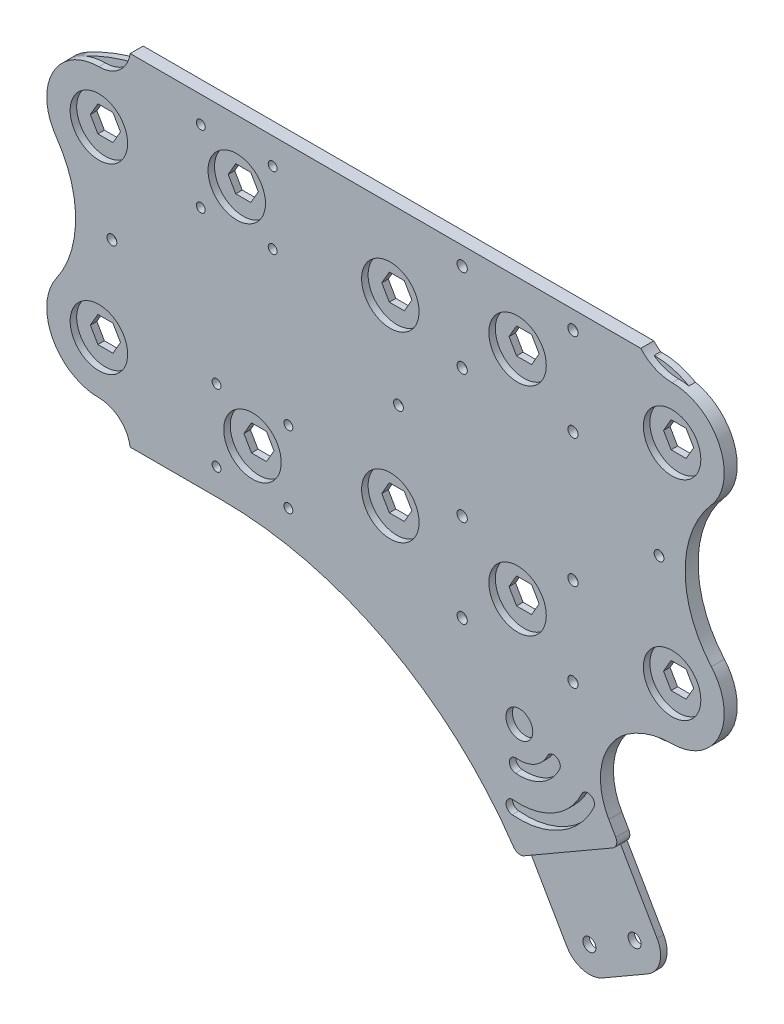
SolidWorks part; units mm, degrees
material "1060 Alloy"
ref_plane "Front Plane" through (0, 0, 0) normal (0, 0, 1) x (1, 0, 0)
ref_plane "Top Plane" through (0, 0, 0) normal (0, 1, 0) x (1, 0, 0)
ref_plane "Right Plane" through (0, 0, 0) normal (1, 0, 0) x (0, 0, -1)
sketch "Sketch1" plane through (0, 0, 0) normal (0, 0, 1) x (1, 0, 0)
  line L9 (183.022, 31.75) -> (225.0336, 31.75)
  line L10 (183.022, 31.75) -> (183.022, 73.7616)
  line L11 (183.022, 73.7616) -> (225.0336, 73.7616)
  line L12 (225.0336, 31.75) -> (225.0336, 73.7616)
  line L13 (183.022, 31.75) -> (225.0336, 73.7616) construction
  line L14 (183.022, 73.7616) -> (225.0336, 31.75) construction
  line L15 (17.8512, 0) -> (50000, 0) construction
  line L16 (46.1727, 31.75) -> (88.1843, 31.75)
  line L17 (46.1727, 31.75) -> (46.1727, 73.7616)
  line L18 (46.1727, 73.7616) -> (88.1843, 73.7616)
  line L19 (88.1843, 31.75) -> (88.1843, 73.7616)
  line L20 (46.1727, 31.75) -> (88.1843, 73.7616) construction
  line L21 (46.1727, 73.7616) -> (88.1843, 31.75) construction
  line L22 (207.694, 59.1058) -> (200.3617, 59.1058)
  line L23 (200.3617, 59.1058) -> (196.6955, 52.7558)
  line L24 (196.6955, 52.7558) -> (200.3617, 46.4058)
  line L25 (200.3617, 46.4058) -> (207.694, 46.4058)
  line L26 (207.694, 46.4058) -> (211.3602, 52.7558)
  line L27 (211.3602, 52.7558) -> (207.694, 59.1058)
  line L28 (74.5108, 52.7558) -> (70.8447, 59.1058)
  line L29 (70.8447, 59.1058) -> (63.5123, 59.1058)
  line L30 (63.5123, 59.1058) -> (59.8461, 52.7558)
  line L31 (59.8461, 52.7558) -> (63.5123, 46.4058)
  line L32 (63.5123, 46.4058) -> (70.8447, 46.4058)
  line L33 (70.8447, 46.4058) -> (74.5108, 52.7558)
  line L34 (3.6662, 50.8) -> (-3.6662, 50.8)
  line L35 (-3.6662, 50.8) -> (-7.3323, 44.45)
  line L36 (-7.3323, 44.45) -> (-3.6662, 38.1)
  line L37 (-3.6662, 38.1) -> (3.6662, 38.1)
  line L38 (3.6662, 38.1) -> (7.3323, 44.45)
  line L39 (7.3323, 44.45) -> (3.6662, 50.8)
  line L40 (282.994, 57.15) -> (275.6617, 57.15)
  line L41 (275.6617, 57.15) -> (271.9955, 50.8)
  line L42 (271.9955, 50.8) -> (275.6617, 44.45)
  line L43 (275.6617, 44.45) -> (282.994, 44.45)
  line L44 (282.994, 44.45) -> (286.6602, 50.8)
  line L45 (286.6602, 50.8) -> (282.994, 57.15)
  line L46 (53.8347, -73.7616) -> (95.8463, -31.75) construction
  line L47 (53.8347, -31.75) -> (95.8463, -73.7616) construction
  line L48 (183.022, -73.7616) -> (225.0336, -31.75) construction
  line L49 (183.022, -31.75) -> (225.0336, -73.7616) construction
  line L50 (286.6602, -50.8) -> (282.994, -57.15)
  line L51 (282.994, -44.45) -> (286.6602, -50.8)
  line L52 (275.6617, -44.45) -> (282.994, -44.45)
  line L53 (271.9955, -50.8) -> (275.6617, -44.45)
  line L54 (275.6617, -57.15) -> (271.9955, -50.8)
  line L55 (282.994, -57.15) -> (275.6617, -57.15)
  line L56 (7.3323, -44.45) -> (3.6662, -50.8)
  line L57 (3.6662, -38.1) -> (7.3323, -44.45)
  line L58 (-3.6662, -38.1) -> (3.6662, -38.1)
  line L59 (-7.3323, -44.45) -> (-3.6662, -38.1)
  line L60 (-3.6662, -50.8) -> (-7.3323, -44.45)
  line L61 (3.6662, -50.8) -> (-3.6662, -50.8)
  line L62 (78.5067, -46.4058) -> (82.1729, -52.7558)
  line L63 (71.1743, -46.4058) -> (78.5067, -46.4058)
  line L64 (67.5082, -52.7558) -> (71.1743, -46.4058)
  line L65 (71.1743, -59.1058) -> (67.5082, -52.7558)
  line L66 (78.5067, -59.1058) -> (71.1743, -59.1058)
  line L67 (82.1729, -52.7558) -> (78.5067, -59.1058)
  line L68 (211.3602, -52.7558) -> (207.694, -59.1058)
  line L69 (207.694, -46.4058) -> (211.3602, -52.7558)
  line L70 (200.3617, -46.4058) -> (207.694, -46.4058)
  line L71 (196.6955, -52.7558) -> (200.3617, -46.4058)
  line L72 (200.3617, -59.1058) -> (196.6955, -52.7558)
  line L73 (207.694, -59.1058) -> (200.3617, -59.1058)
  line L74 (95.8463, -31.75) -> (95.8463, -73.7616)
  line L75 (53.8347, -73.7616) -> (95.8463, -73.7616)
  line L76 (53.8347, -31.75) -> (53.8347, -73.7616)
  line L77 (53.8347, -31.75) -> (95.8463, -31.75)
  line L78 (225.0336, -31.75) -> (225.0336, -73.7616)
  line L79 (183.022, -73.7616) -> (225.0336, -73.7616)
  line L80 (183.022, -31.75) -> (183.022, -73.7616)
  line L81 (183.022, -31.75) -> (225.0336, -31.75)
  line L82 (39.8227, 80.1116) -> (268.1917, 80.1116)
  line L83 (88.1843, 73.7616) -> (183.022, 73.7616) construction
  line L96 (39.8227, -80.1116) -> (131.769, -80.1116)
  line L97 (175.7631, -105.5116) -> (224.8617, -190.5527)
  line L98 (230.7557, -99.1616) -> (268.8557, -165.1527)
  line L99 (242.2102, -195.2013) -> (264.2072, -182.5013)
  line L100 (253.2087, -188.8513) -> (190.4278, -80.1116) construction
  line L101 (131.769, -80.1116) -> (241.7543, -80.1116) construction
  line L102 (230.7557, -99.1616) -> (186.7617, -124.5616) construction
  line L103 (205.8117, -157.5572) -> (249.8057, -132.1572) construction
  line L104 (224.8617, -190.5527) -> (268.8557, -165.1527) construction
  line L105 (197.7602, -118.2116) -> (235.8602, -184.2027) construction
  line L106 (219.7572, -105.5116) -> (257.8572, -171.5027) construction
  line L107 (268.1917, -80.1116) -> (241.7543, -80.1116)
  line L108 (177.0278, 31.3058) -> (231.0278, 74.2058) construction
  line L109 (149.3514, -44.45) -> (145.6852, -50.8)
  line L110 (145.6852, 50.8) -> (138.3528, 50.8)
  line L111 (138.3528, 50.8) -> (134.6867, 44.45)
  line L112 (134.6867, 44.45) -> (138.3528, 38.1)
  line L113 (138.3528, 38.1) -> (145.6852, 38.1)
  line L114 (145.6852, 38.1) -> (149.3514, 44.45)
  line L115 (149.3514, 44.45) -> (145.6852, 50.8)
  line L122 (145.6852, -38.1) -> (149.3514, -44.45)
  line L123 (138.3528, -38.1) -> (145.6852, -38.1)
  line L124 (134.6867, -44.45) -> (138.3528, -38.1)
  line L125 (138.3528, -50.8) -> (134.6867, -44.45)
  line L126 (145.6852, -50.8) -> (138.3528, -50.8)
  line L127 (204.0278, 105.5116) -> (204.0278, 0) construction
  line L129 (180.4117, -113.5631) -> (256.6117, -245.5453) construction
  line L130 (180.4117, -113.5631) -> (224.4057, -88.1631) construction
  line L131 (256.6117, -245.5453) -> (300.6057, -220.1453) construction
  line L132 (224.4057, -88.1631) -> (300.6057, -220.1453) construction
  line L133 (180.4117, -113.5631) -> (300.6057, -220.1453) construction
  line L134 (256.6117, -245.5453) -> (224.4057, -88.1631) construction
  line L135 (28.4347, -54.7116) -> (53.8347, -54.7116)
  line L136 (88.1843, 80.1116) -> (113.5843, 80.1116)
  line L137 (88.1843, 80.1116) -> (88.1843, 54.7116)
  line L138 (88.1843, 54.7116) -> (113.5843, 54.7116)
  line L139 (113.5843, 80.1116) -> (113.5843, 54.7116)
  line L140 (28.4347, -54.7116) -> (28.4347, -80.1116)
  line L141 (28.4347, -80.1116) -> (53.8347, -80.1116)
  line L142 (53.8347, -54.7116) -> (53.8347, -80.1116)
  circle A0 centre (0, 44.45) radius 25.4 construction
  circle A1 centre (67.1785, 52.7558) radius 17.5
  circle A2 centre (204.0278, 52.7558) radius 30
  circle A3 centre (279.3278, 50.8) radius 38.1 construction
  circle A4 centre (0, 44.45) radius 14
  circle A5 centre (67.1785, 52.7558) radius 14
  circle A6 centre (204.0278, 52.7558) radius 14
  circle A7 centre (279.3278, 50.8) radius 14
  circle A8 centre (204.0278, 52.7558) radius 6.35 construction
  circle A9 centre (67.1785, 52.7558) radius 6.35 construction
  circle A10 centre (0, 44.45) radius 6.35 construction
  circle A11 centre (279.3278, 50.8) radius 6.35 construction
  circle A12 centre (279.3278, -50.8) radius 6.35 construction
  circle A13 centre (0, -44.45) radius 6.35 construction
  circle A14 centre (74.8405, -52.7558) radius 6.35 construction
  circle A15 centre (204.0278, -52.7558) radius 6.35 construction
  circle A16 centre (279.3278, -50.8) radius 14
  circle A17 centre (204.0278, -52.7558) radius 14
  circle A18 centre (74.8405, -52.7558) radius 14
  circle A19 centre (0, -44.45) radius 14
  circle A20 centre (279.3278, -50.8) radius 38.1 construction
  circle A21 centre (204.0278, -52.7558) radius 30
  circle A22 centre (74.8405, -52.7558) radius 17.5
  circle A23 centre (0, -44.45) radius 25.4 construction
  circle A26 centre (142.019, 44.45) radius 25.4 construction
  arc A37 (175.7631, -105.5116) -> (131.769, -80.1116) centre (131.769, -130.9116) ccw
  arc A38 (230.7557, -99.1616) -> (241.7543, -80.1116) centre (241.7543, -92.8116) cw
  circle A39 centre (197.7602, -118.2116) radius 3.175
  circle A40 centre (219.7572, -105.5116) radius 3.175
  circle A43 centre (216.8102, -151.2072) radius 3.175
  circle A44 centre (238.8072, -138.5072) radius 3.175
  circle A45 centre (235.8602, -184.2027) radius 3.175
  circle A46 centre (257.8572, -171.5027) radius 3.175
  arc A47 (268.8557, -165.1527) -> (264.2072, -182.5013) centre (257.8572, -171.5027) cw
  arc A48 (224.8617, -190.5527) -> (242.2102, -195.2013) centre (235.8602, -184.2027) ccw
  circle A49 centre (0, 44.45) radius 20.35
  arc A50 (39.8227, 80.1116) -> (-12.2752, 66.6869) centre (39.8227, -27.6901) ccw
  arc A51 (284.0457, 20.8532) -> (268.1917, 80.1116) centre (268.1917, 48.3616) ccw
  arc A52 (284.0457, 20.8532) -> (271.9955, 0) centre (296.0641, 0) ccw
  circle A53 centre (0, -44.45) radius 20.35
  arc A54 (39.8227, -80.1116) -> (-12.2752, -66.6869) centre (39.8227, 27.6901) cw
  arc A55 (-12.2752, 66.6869) -> (-12.8954, 22.5669) centre (0, 44.45) ccw
  arc A56 (284.0457, -20.8532) -> (271.9955, 0) centre (296.0641, 0) cw
  arc A57 (-12.8954, 22.5669) -> (0, 0) centre (-26.1938, 0) cw
  arc A58 (-12.8954, -22.5669) -> (0, 0) centre (-26.1938, 0) ccw
  arc A59 (284.0457, -20.8532) -> (268.1917, -80.1116) centre (268.1917, -48.3616) cw
  circle A60 centre (279.3278, 50.8) radius 20.35
  circle A61 centre (279.3278, -50.8) radius 20.35
  circle A64 centre (67.1785, 52.7558) radius 24.7523 construction
  circle A67 centre (231.0278, 74.2058) radius 2.5
  circle A68 centre (177.0278, 31.3058) radius 2.5
  circle A69 centre (142.019, 44.45) radius 14
  circle A70 centre (142.019, 44.45) radius 6.35 construction
  circle A71 centre (142.019, -44.45) radius 14
  circle A72 centre (142.019, -44.45) radius 25.4 construction
  circle A73 centre (231.0278, -74.2058) radius 2.5
  circle A74 centre (177.0278, -31.3058) radius 2.5
  circle A75 centre (49.676, 70.2583) radius 2.159
  circle A76 centre (84.681, 35.2533) radius 2.159
  circle A77 centre (92.343, -35.2533) radius 2.159
  circle A78 centre (57.338, -70.2583) radius 2.159
  circle A79 centre (177.0278, 74.2058) radius 2.5
  circle A80 centre (231.0278, 31.3058) radius 2.5
  circle A81 centre (231.0278, -31.3058) radius 2.5
  circle A82 centre (177.0278, -74.2058) radius 2.5
  circle A83 centre (49.676, 35.2533) radius 2.159
  circle A84 centre (84.681, 70.2583) radius 2.159
  circle A85 centre (92.343, -70.2583) radius 2.159
  circle A86 centre (57.338, -35.2533) radius 2.159
  arc A87 (-12.2752, -66.6869) -> (-12.8954, -22.5669) centre (0, -44.45) cw
  circle A88 centre (0, 44.45) radius 38.1 construction
  circle A89 centre (0, -44.45) radius 38.1 construction
  point P6 (204.0278, 52.7558)
  point P17 (0, 19.05)
  point P18 (279.3278, 88.9)
  point P28 (279.3278, 12.7)
  point P108 (279.3278, -12.7)
  point P110 (279.3278, -88.9)
  point P111 (0, -19.05)
  point P112 (204.0278, -52.7558)
  point P124 (142.019, 19.05)
  point P171 (216.8102, -151.2072)
  point P174 (232.5732, -196.47)
  point P207 (204.0278, 52.7558)
  point P213 (204.0278, 52.7558)
  point P224 (67.1785, 52.7558)
  point P233 (240.5087, -166.8542)
  dimension "D1" = 50.8
  dimension "D2" = 76.2
  dimension "D4" = 35
  dimension "D5" = 60
  dimension "D9" = 28
  dimension "D10" = 28
  dimension "D12" = 28
  dimension "D7" = 6.35
  dimension "D21" = 6.35
  dimension "D22" = 6.35
  dimension "D23" = 6.35
  dimension "D24" = 12.7
  dimension "D28" = 50.8
  dimension "D29" = 12.7
  dimension "D31" = 6.35
  dimension "D35" = 12.7
  dimension "D34" = 12.7
  dimension "D36" = 31.75
  dimension "D37" = 4.318
  dimension "D38" = 49.5046
  dimension "D41" = 5
  dimension "D42" = 50.8
  dimension "D45" = 4.318
  dimension "D54" = 3.5033
  dimension "D55" = 3.5033
  dimension "D56" = 3.5033
  dimension "D57" = 3.5033
  dimension "D58" = 3.5033
  dimension "D59" = 3.5033
  dimension "D60" = 3.5033
  dimension "D61" = 3.5033
  dimension "D3" = 19.05
  dimension "D6" = 42.0116
  dimension "D8" = 42.0116
  dimension "D11" = 67.69
  dimension "D13" = 75.3
  dimension "D14" = 279.4
  dimension "D15" = 12.7
  dimension "D16" = 12.7
  dimension "D17" = 12.7
  dimension "D18" = 12.7
  dimension "D19" = 12.7
  dimension "D20" = 31.75
  dimension "D25" = 50.8
  dimension "D26" = 30
  dimension "D27" = 76.2
  dimension "D30" = 88.9
  dimension "D32" = 12.7
  dimension "D33" = 12.7
  dimension "D39" = 42.9
  dimension "D40" = 54
  dimension "D43" = 75.3
  dimension "D44" = 19.05
  dimension "D46" = 50.8
  dimension "D47" = 152.4
  dimension "D48" = 12.7
  dimension "D49" = 25.4
  dimension "D50" = 3.5033
  dimension "D51" = 3.5033
  dimension "D52" = 3.5033
  dimension "D53" = 3.5033
  dimension "D62" = 25.4
  dimension "D63" = 75.3
sketch "Sketch2" plane through (0, 0, 0) normal (0, 0, 1) x (1, 0, 0)
  line L0 (-130.0566, 0) -> (174.7434, 0) construction
  line L1 (-199982.1488, 0) -> (250000, 0) construction
  line L2 (-130.0566, 25.4) -> (174.7434, 25.4)
  line L3 (-130.0566, -25.4) -> (174.7434, -25.4)
  arc A0 (-130.0566, 25.4) -> (-130.0566, -25.4) centre (-130.0566, 0) ccw
  arc A1 (174.7434, -25.4) -> (174.7434, 25.4) centre (174.7434, 0) ccw
  point P4 (22.3434, 0)
  point P9 (-155.4566, 0)
  point P10 (200.1434, 0)
  dimension "D1" = 25.4
  dimension "D2" = 355.6
extrude "Boss-Extrude3" add sketch "Sketch1" along normal blind 3.175
sketch "Sketch3" [suppressed] plane through (0, 0, 0) normal (0, 0, 1) x (1, 0, 0)
  line L0 (-3.6662, 50.8) -> (3.6662, 38.1) construction
  line L1 (63.5123, 59.1058) -> (70.8447, 46.4058) construction
  line L2 (138.3528, 50.8) -> (145.6852, 38.1) construction
  line L3 (188.9164, 59.1058) -> (196.2487, 46.4058) construction
  line L4 (256.6064, 57.15) -> (263.9387, 44.45) construction
  line L5 (0, 0) -> (252.9402, 0) construction
  circle A0 centre (0, 44.45) radius 14.2875
  circle A1 centre (67.1785, 52.7558) radius 14.2875
  circle A2 centre (142.019, 44.45) radius 14.2875
  circle A3 centre (192.5825, 52.7558) radius 14.2875
  circle A4 centre (260.2725, 50.8) radius 14.2875
  arc A5 (264.9904, 20.8532) -> (264.9904, -20.8532) centre (277.0088, 0) ccw construction
  circle A6 centre (260.2725, -50.8) radius 14.2875
  circle A7 centre (192.5825, -52.7558) radius 14.2875
  circle A8 centre (142.019, -44.45) radius 14.2875
  circle A9 centre (67.1785, -52.7558) radius 14.2875
  circle A10 centre (0, -44.45) radius 14.2875
  dimension "D1" = 28.575
extrude "Cut-Extrude1" [suppressed] cut sketch "Sketch3" along normal blind 3.175
sketch "Sketch4" plane through (0, 0, 0) normal (0, 0, 1) x (1, 0, 0)
  line L0 (248.4449, -180.6001) -> (-24751.5551, 43120.6701) construction
  line L1 (-14, 76.7058) -> (293.3278, 76.7058) construction
  line L2 (-14, 76.7058) -> (-14, -76.7058) construction
  line L3 (-14, -76.7058) -> (293.3278, -76.7058) construction
  line L4 (293.3278, 76.7058) -> (293.3278, -76.7058) construction
  line L5 (-31.75, 44.45) -> (-31.75, 50044.45) construction
  line L6 (113.6599, -691.382) -> (113.6599, 49308.618) construction
  line L7 (-14, 83.0558) -> (293.3278, 83.0558) construction
  line L8 (-14, -83.0558) -> (293.3278, -83.0558) construction
  line L9 (242.2102, -195.2013) -> (264.2072, -182.5013) construction
  line L10 (202.3718, -157.9492) -> (251.8651, -129.3742) construction
  line L11 (0, 44.45) -> (0, -44.45) construction
  line L12 (279.3278, 50.8) -> (279.3278, -50.8) construction
  line L13 (0, 0) -> (279.3278, 0) construction
  line L14 (-14, -76.7058) -> (-14, -83.0558) construction
  line L15 (-14, -79.8808) -> (293.3278, -79.8808) construction
  line L20 (251.8651, -129.3742) -> (264.5651, -151.3712) construction
  line L21 (264.5651, -151.3712) -> (215.0718, -179.9462) construction
  line L22 (215.0718, -179.9462) -> (202.3718, -157.9492) construction
  line L23 (293.3278, -76.7058) -> (293.3278, -83.0558) construction
  line L24 (202.3718, -157.9492) -> (173.7968, -108.4558) construction
  line L25 (173.7968, -108.4558) -> (223.2901, -79.8808) construction
  line L26 (223.2901, -79.8808) -> (251.8651, -129.3742) construction
  line L27 (180.1468, -119.4543) -> (229.6401, -90.8793) construction
  line L28 (15.24, 83.0558) -> (264.0878, 83.0558)
  line L29 (298.4648, 34.0986) -> (298.4648, -34.0986) construction
  line L30 (-20.775, 29.8363) -> (-20.775, -29.8363) construction
  line L31 (15.24, 83.0558) -> (15.24, -83.0558) construction
  line L32 (15.24, -83.0558) -> (59.9527, -83.0558)
  line L33 (208.7218, -168.9477) -> (215.0718, -179.9462)
  line L34 (215.0718, -179.9462) -> (264.5651, -151.3712)
  line L35 (264.5651, -151.3712) -> (248.5101, -123.563)
  line L36 (204.8935, -105.1668) -> (201.6835, -141.8567) construction
  circle A0 centre (0, 44.45) radius 14
  circle A1 centre (142.019, 44.45) radius 14
  circle A2 centre (279.3278, 50.8) radius 14
  circle A3 centre (279.3278, -50.8) radius 14
  circle A4 centre (142.019, -44.45) radius 14
  circle A5 centre (0, -44.45) radius 14
  circle A6 centre (67.1785, 52.7558) radius 14
  circle A7 centre (204.0278, 52.7558) radius 14
  circle A8 centre (204.0278, -52.7558) radius 14
  circle A9 centre (74.8405, -52.7558) radius 14
  circle A11 centre (0, 44.45) radius 31.75 construction
  circle A12 centre (6.35, 0) radius 2.3813
  circle A13 centre (272.9778, 0) radius 2.3813
  circle A14 centre (145.9778, 0) radius 2.3813
  circle A16 centre (92.343, -70.2583) radius 2.159 construction
  circle A17 centre (57.338, -70.2583) radius 2.159 construction
  circle A18 centre (57.338, -35.2533) radius 2.159 construction
  circle A19 centre (92.343, -35.2533) radius 2.159 construction
  circle A20 centre (177.0278, -74.2058) radius 2.5 construction
  circle A21 centre (231.0278, -74.2058) radius 2.5 construction
  circle A22 centre (231.0278, -31.3058) radius 2.5 construction
  circle A23 centre (177.0278, -31.3058) radius 2.5 construction
  circle A24 centre (231.0278, 31.3058) radius 2.5 construction
  circle A25 centre (231.0278, 74.2058) radius 2.5 construction
  circle A26 centre (177.0278, 31.3058) radius 2.5 construction
  circle A27 centre (177.0278, 74.2058) radius 2.5 construction
  circle A28 centre (49.676, 35.2533) radius 2.159 construction
  circle A29 centre (84.681, 35.2533) radius 2.159 construction
  circle A30 centre (84.681, 70.2583) radius 2.159 construction
  circle A31 centre (49.676, 70.2583) radius 2.159 construction
  circle A38 centre (92.343, -70.2583) radius 2.159
  circle A39 centre (57.338, -70.2583) radius 2.159
  circle A40 centre (57.338, -35.2533) radius 2.159
  circle A41 centre (92.343, -35.2533) radius 2.159
  circle A42 centre (177.0278, -74.2058) radius 2.5
  circle A43 centre (231.0278, -74.2058) radius 2.5
  circle A44 centre (231.0278, -31.3058) radius 2.5
  circle A45 centre (177.0278, -31.3058) radius 2.5
  circle A46 centre (231.0278, 31.3058) radius 2.5
  circle A47 centre (231.0278, 74.2058) radius 2.5
  circle A48 centre (177.0278, 31.3058) radius 2.5
  circle A49 centre (177.0278, 74.2058) radius 2.5
  circle A50 centre (49.676, 35.2533) radius 2.159
  circle A51 centre (84.681, 35.2533) radius 2.159
  circle A52 centre (84.681, 70.2583) radius 2.159
  circle A53 centre (49.676, 70.2583) radius 2.159
  circle A54 centre (0, 44.45) radius 25.4 construction
  circle A55 centre (0, -44.45) radius 25.4 construction
  circle A56 centre (279.3278, 50.8) radius 38.1 construction
  circle A58 centre (279.3278, -50.8) radius 38.1 construction
  circle A62 centre (279.3278, 50.8) radius 25.4 construction
  circle A63 centre (279.3278, -50.8) radius 25.4 construction
  arc A64 (279.3278, 76.2) -> (298.4648, 34.0986) centre (279.3278, 50.8) cw
  arc A65 (298.4648, -34.0986) -> (279.3278, -76.2) centre (279.3278, -50.8) cw
  arc A66 (298.4648, 34.0986) -> (298.4648, -34.0986) centre (337.5362, 0) ccw
  arc A67 (264.0878, 83.0558) -> (279.3278, 76.2) centre (279.3278, 96.5667) ccw
  arc A68 (15.24, 83.0558) -> (0, 69.85) centre (0, 85.2467) cw
  arc A69 (0, 69.85) -> (-20.775, 29.8363) centre (0, 44.45) ccw
  arc A70 (-20.775, 29.8363) -> (-20.775, -29.8363) centre (-63.1906, 0) cw
  arc A71 (-20.775, -29.8363) -> (0, -69.85) centre (0, -44.45) ccw
  arc A72 (0, -69.85) -> (15.24, -83.0558) centre (0, -85.2467) cw
  arc A73 (59.9527, -83.0558) -> (208.7218, -168.9477) centre (59.9527, -254.8395) cw
  arc A78 (279.3278, -76.2) -> (257.5239, -83.0558) centre (279.3278, -114.3) ccw
  arc A79 (257.5239, -83.0558) -> (248.5101, -123.563) centre (275.0849, -108.2201) ccw
  circle A80 centre (204.8935, -105.1668) radius 6.5481
  arc A81 (201.6835, -141.8567) -> (238.2728, -120.7319) centre (204.8935, -105.1668) ccw construction
  arc A82 (201.3991, -145.1082) -> (241.2309, -122.1112) centre (204.8935, -105.1668) ccw
  arc A83 (201.968, -138.6052) -> (235.3147, -119.3525) centre (204.8935, -105.1668) ccw
  arc A84 (201.968, -138.6052) -> (201.3991, -145.1082) centre (201.6835, -141.8567) ccw
  arc A85 (241.2309, -122.1112) -> (235.3147, -119.3525) centre (238.2728, -120.7319) ccw
  arc A86 (203.2885, -123.5117) -> (221.5831, -112.9493) centre (204.8935, -105.1668) ccw construction
  arc A87 (203.004, -126.7632) -> (224.5412, -114.3287) centre (204.8935, -105.1668) ccw
  arc A88 (203.573, -120.2603) -> (218.625, -111.57) centre (204.8935, -105.1668) ccw
  arc A89 (203.573, -120.2603) -> (203.004, -126.7632) centre (203.2885, -123.5117) ccw
  arc A90 (224.5412, -114.3287) -> (218.625, -111.57) centre (221.5831, -112.9493) ccw
  point P100 (253.2087, -188.8513)
  point P118 (223.3085, -137.0625)
  point P124 (227.1185, -143.6617)
  point P138 (279.3278, -76.2)
  point P139 (285.6778, 0)
  point P148 (0, -69.85)
  point P160 (214.101, -121.1147)
  dimension "D1" = 28
  dimension "D2" = 50.8
  dimension "D3" = 76.2
  dimension "D7" = 4.7625
  dimension "D12" = 127
  dimension "D13" = 7.62
  dimension "D19" = 15.24
  dimension "D21" = 38.1
  dimension "D16" = 13.0962
  dimension "D24" = 6.5278
  dimension "D5" = 145.4099
  dimension "D6" = 150
  dimension "D10" = 6.35
  dimension "D11" = 6.35
  dimension "D14" = 25.4
  dimension "D15" = 57.15
  dimension "D17" = 57.15
  dimension "D18" = 6.35
  dimension "D20" = 15.24
  dimension "D22" = 248.8478
  dimension "D23" = 12.7
  dimension "D26" = 6.5278
  dimension "D27" = 35
  dimension "D4" = 6.35
  dimension "D8" = 6.35
  dimension "D9" = 6.35
extrude "Boss-Extrude4" add sketch "Sketch4" along normal blind 6.35 separate body
fillet "Fillet1" radius 2.54 2 edges at (264.5651, -151.3712, 3.175) (215.0718, -179.9462, 3.175)
sketch "Sketch5" plane through (0, 0, 6.35) normal (0, 0, 1) x (1, 0, 0)
  line L7 (263.2951, -149.1715) -> (248.5101, -123.563) construction
  line L8 (217.2715, -178.6762) -> (262.3654, -152.6412) construction
  line L9 (208.7218, -168.9477) -> (213.8018, -177.7465) construction
  line L10 (263.2951, -149.1715) -> (253.7701, -132.6737)
  line L11 (217.2715, -178.6762) -> (262.3654, -152.6412)
  line L12 (208.7218, -168.9477) -> (213.8018, -177.7465)
  line L13 (204.0774, -161.3638) -> (253.7701, -132.6737)
  arc A1 (262.3654, -152.6412) -> (263.2951, -149.1715) centre (261.0954, -150.4415) ccw construction
  arc A2 (213.8018, -177.7465) -> (217.2715, -178.6762) centre (216.0015, -176.4765) ccw construction
  arc A3 (208.7218, -168.9477) -> (59.9527, -83.0558) centre (59.9527, -254.8395) ccw construction
  arc A5 (262.3654, -152.6412) -> (263.2951, -149.1715) centre (261.0954, -150.4415) ccw
  arc A6 (213.8018, -177.7465) -> (217.2715, -178.6762) centre (216.0015, -176.4765) ccw
  arc A7 (208.7218, -168.9477) -> (204.0774, -161.3638) centre (59.9527, -254.8395) ccw
  dimension "D1" = 21.59
extrude "Cut-Extrude2" cut sketch "Sketch5" against normal through all both
fillet "Fillet2" radius 3.81 2 edges at (204.0774, -161.3638, 3.175) (253.7701, -132.6737, 3.175)
